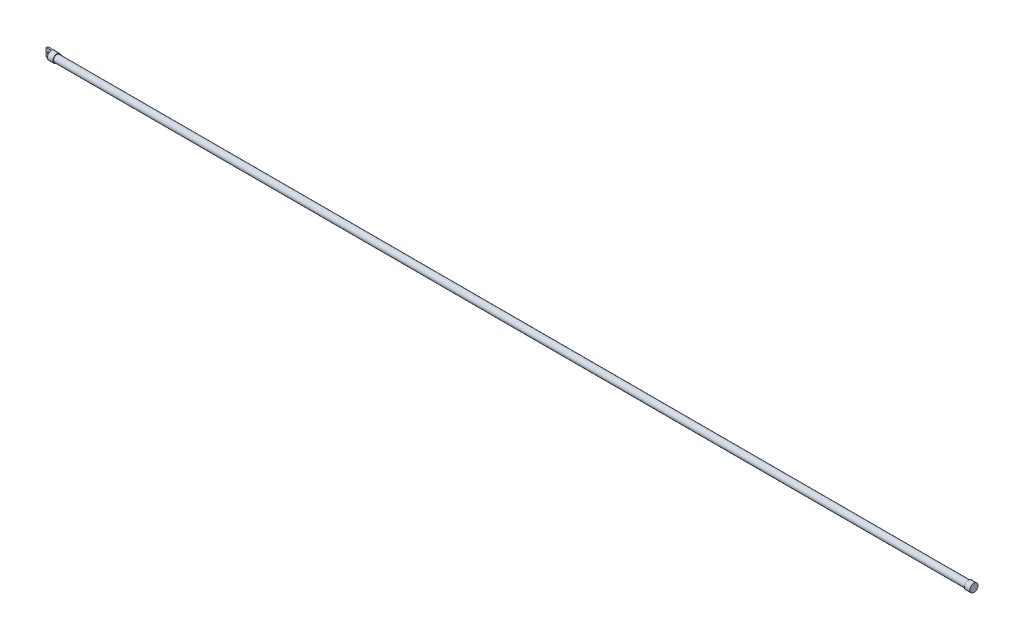
SolidWorks part; units mm, degrees
material "A-Glass Fiber"
ref_plane "Front Plane" through (0, 0, 0) normal (0, 0, 1) x (1, 0, 0)
ref_plane "Top Plane" through (0, 0, 0) normal (0, 1, 0) x (1, 0, 0)
ref_plane "Right Plane" through (0, 0, 0) normal (1, 0, 0) x (0, 0, -1)
sketch "Sketch1" plane through (0, 0, 0) normal (1, 0, 0) x (0, 0, -1)
  circle A0 centre (0, 0) radius 15.875
  dimension "D1" = 31.75
extrude "Boss-Extrude1" add sketch "Sketch1" along normal blind 4267.2
sketch "Sketch2" plane through (4267.2, 0, 0) normal (1, 0, 0) x (0, 0, -1)
  circle A0 centre (0, 0) radius 19.05
  dimension "D1" = 38.1
extrude "Boss-Extrude2" add sketch "Sketch2" against normal blind 25.4
sketch "Sketch3" plane through (0, 0, 0) normal (-1, 0, 0) x (0, 0, 1)
  circle A0 centre (0, 0) radius 19.05
  dimension "D1" = 38.1
extrude "Boss-Extrude3" add sketch "Sketch3" along normal blind 50.8
sketch "Sketch4" plane through (-50.8, 0, 0) normal (-1, 0, 0) x (0, 0, 1)
  line L0 (0, 0) -> (0, 36.2312) construction
  line L1 (0, 36.2312) -> (0, -26.6589) construction
  line L3 (0, 26.5279) -> (29.0974, 26.5279)
  line L4 (0, 26.5279) -> (0, -24.1083)
  line L5 (0, -24.1083) -> (29.0974, -24.1083)
  line L6 (29.0974, 26.5279) -> (29.0974, -24.1083)
extrude "Cut-Extrude1" cut sketch "Sketch4" against normal blind 25.4
sketch "Sketch5" plane through (0, 0, 0) normal (0, 0, 1) x (1, 0, 0)
  line L0 (-50.8, 19.05) -> (-50.8, -19.05) construction
  line L1 (-50.8, 19.05) -> (-25.4, 19.05) construction
  circle A0 centre (-38.1, 0) radius 6.35
  dimension "D1" = 12.7
  dimension "D2" = 12.7
  dimension "D3" = 19.05
extrude "Cut-Extrude2" cut sketch "Sketch5" against normal through all
